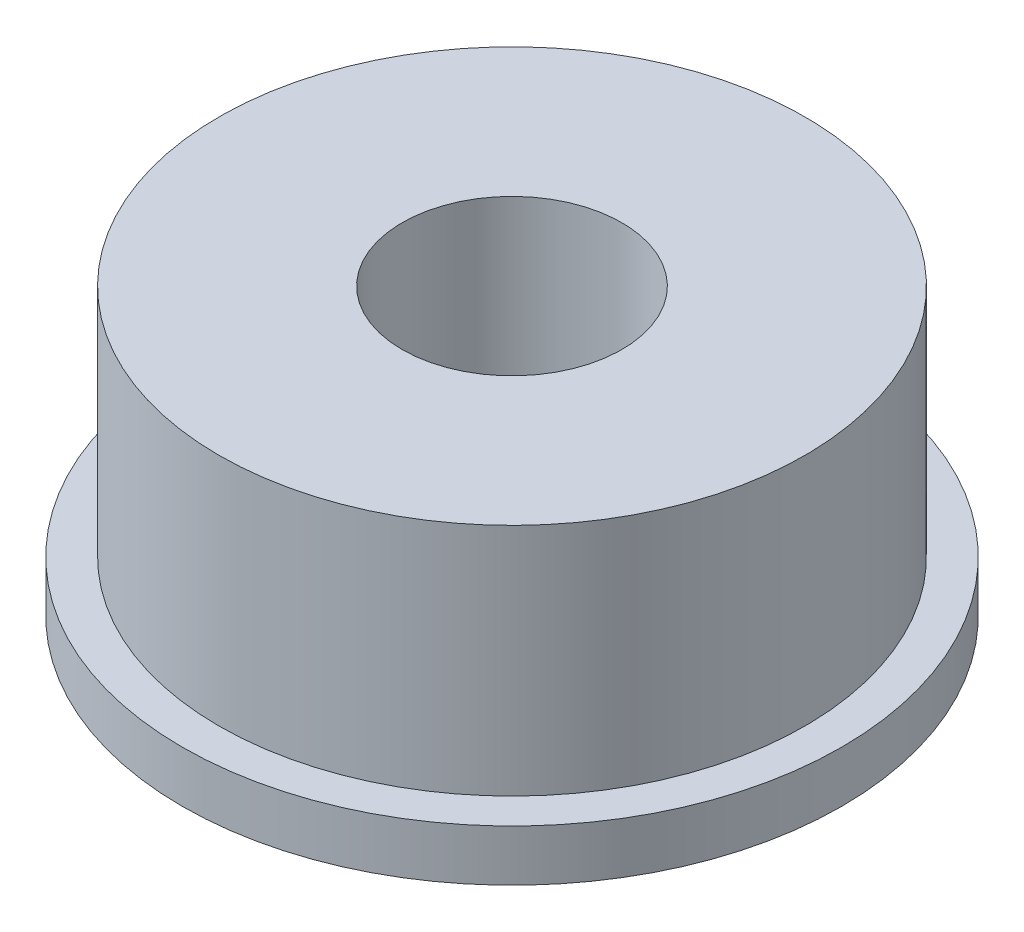
SolidWorks part; units mm, degrees
ref_plane "Front Plane" through (0, 0, 0) normal (0, 0, 1) x (1, 0, 0)
ref_plane "Top Plane" through (0, 0, 0) normal (0, 1, 0) x (1, 0, 0)
ref_plane "Right Plane" through (0, 0, 0) normal (1, 0, 0) x (0, 0, -1)
sketch "Sketch1" plane through (0, 0, 0) normal (0, 1, 0) x (1, 0, 0)
  circle A0 centre (0, 0) radius 4.5
  dimension "D1" = 9
extrude "Boss-Extrude1" add sketch "Sketch1" along normal blind 0.7
sketch "Sketch2" plane through (0, 0.7, 0) normal (0, 1, 0) x (1, 0, 0)
  circle A0 centre (0, 0) radius 4
  dimension "D1" = 8
extrude "Boss-Extrude2" add sketch "Sketch2" along normal blind 3.2
sketch "Sketch3" plane through (0, 3.9, 0) normal (0, 1, 0) x (1, 0, 0)
  circle A0 centre (0, 0) radius 1.5
  dimension "D1" = 3
extrude "Cut-Extrude1" cut sketch "Sketch3" against normal through all
